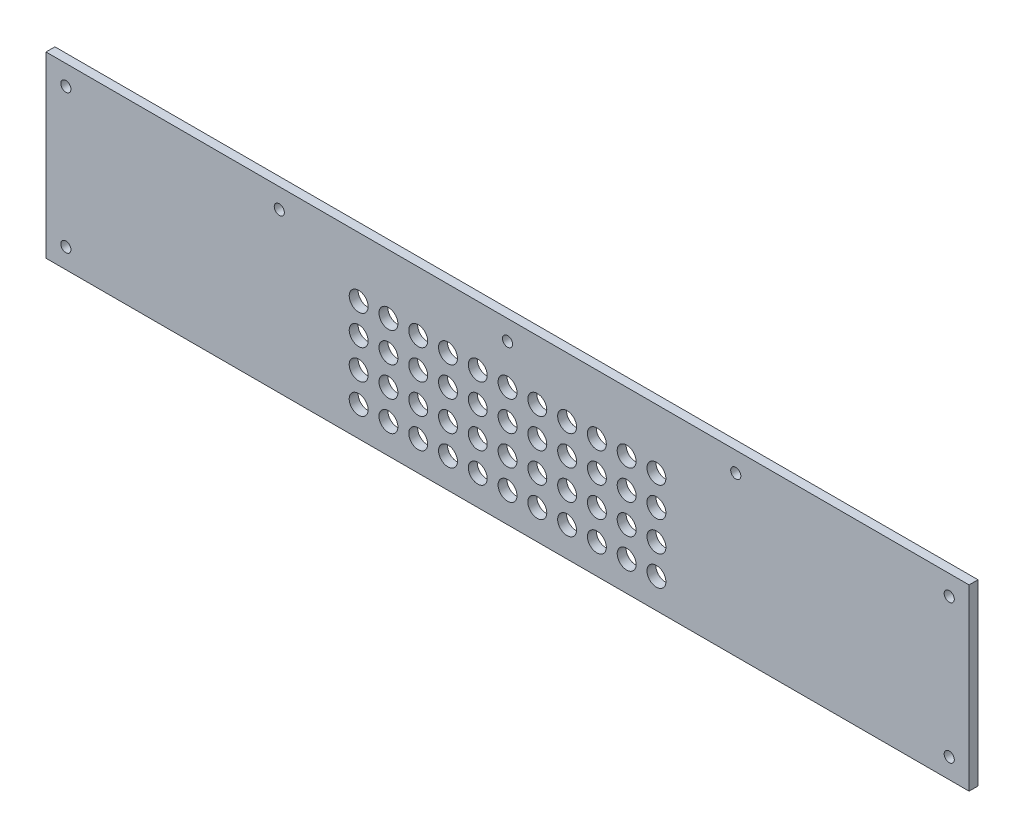
SolidWorks part; units mm, degrees
material "Acrylic (Medium-high impact)"
ref_plane "Front Plane" through (0, 0, 0) normal (0, 0, 1) x (1, 0, 0)
ref_plane "Top Plane" through (0, 0, 0) normal (0, 1, 0) x (1, 0, 0)
ref_plane "Right Plane" through (0, 0, 0) normal (1, 0, 0) x (0, 0, -1)
sketch "Sketch1" plane through (0, 0, 0) normal (0, 0, 1) x (1, 0, 0)
  line L0 (-222.5, 45) -> (-222.5, -45) construction
  line L1 (-232.5, -45) -> (232.5, -45)
  line L2 (-232.5, -45) -> (-232.5, 45)
  line L3 (-232.5, 45) -> (232.5, 45)
  line L4 (232.5, -45) -> (232.5, 45)
  line L5 (-232.5, -45) -> (232.5, 45) construction
  line L6 (-232.5, 45) -> (232.5, -45) construction
  line L7 (0, 45) -> (0, -45) construction
  line L8 (-232.5, 35) -> (2.55, 35) construction
  circle A0 centre (-222.5, 35) radius 2.55
  circle A1 centre (-222.5, -35) radius 2.55
  circle A2 centre (0, 35) radius 2.55
  circle A3 centre (-114.975, 35) radius 2.55
  circle A4 centre (222.5, -35) radius 2.55
  circle A5 centre (222.5, 35) radius 2.55
  circle A6 centre (114.975, 35) radius 2.55
  point P0 (0, 0)
  point P17 (-114.975, 35)
  dimension "D4" = 5.1
  dimension "D5" = 10
  dimension "D6" = 10
  dimension "D7" = 10
  dimension "D1" = 465
  dimension "D2" = 90
  dimension "D3" = 10
extrude "Boss-Extrude1" add sketch "Sketch1" along normal mid plane 4.4958
sketch "Sketch2" plane through (0, 0, 2.2479) normal (0, 0, 1) x (1, 0, 0)
  line L0 (0, 45) -> (0, -45) construction
  line L1 (232.5, 45) -> (-232.5, 45) construction
  line L2 (-232.5, -45) -> (232.5, -45) construction
  circle A0 centre (0, 15) radius 4.7625
  circle A1 centre (15, 15) radius 4.7625
  circle A2 centre (30, 15) radius 4.7625
  circle A3 centre (45, 15) radius 4.7625
  circle A4 centre (60, 15) radius 4.7625
  circle A5 centre (75, 15) radius 4.7625
  circle A6 centre (15, 0) radius 4.7625
  circle A7 centre (30, 0) radius 4.7625
  circle A8 centre (45, 0) radius 4.7625
  circle A9 centre (60, 0) radius 4.7625
  circle A10 centre (75, 0) radius 4.7625
  circle A11 centre (15, -15) radius 4.7625
  circle A12 centre (30, -15) radius 4.7625
  circle A13 centre (45, -15) radius 4.7625
  circle A14 centre (60, -15) radius 4.7625
  circle A15 centre (75, -15) radius 4.7625
  circle A16 centre (15, -30) radius 4.7625
  circle A17 centre (30, -30) radius 4.7625
  circle A18 centre (45, -30) radius 4.7625
  circle A19 centre (60, -30) radius 4.7625
  circle A20 centre (75, -30) radius 4.7625
  circle A21 centre (0, 0) radius 4.7625
  circle A22 centre (0, -15) radius 4.7625
  circle A23 centre (0, -30) radius 4.7625
  circle A24 centre (-75, -30) radius 4.7625
  circle A25 centre (-60, -30) radius 4.7625
  circle A26 centre (-45, -30) radius 4.7625
  circle A27 centre (-30, -30) radius 4.7625
  circle A28 centre (-15, -30) radius 4.7625
  circle A29 centre (-75, -15) radius 4.7625
  circle A30 centre (-60, -15) radius 4.7625
  circle A31 centre (-45, -15) radius 4.7625
  circle A32 centre (-30, -15) radius 4.7625
  circle A33 centre (-15, -15) radius 4.7625
  circle A34 centre (-75, 0) radius 4.7625
  circle A35 centre (-60, 0) radius 4.7625
  circle A36 centre (-45, 0) radius 4.7625
  circle A37 centre (-30, 0) radius 4.7625
  circle A38 centre (-15, 0) radius 4.7625
  circle A39 centre (-75, 15) radius 4.7625
  circle A40 centre (-60, 15) radius 4.7625
  circle A41 centre (-45, 15) radius 4.7625
  circle A42 centre (-30, 15) radius 4.7625
  circle A43 centre (-15, 15) radius 4.7625
  dimension "D1" = 9.525
  dimension "D2" = 30
  dimension "D6" = 15
  dimension "D5" = 15
  dimension "D3" = 6
  dimension "D4" = 4
extrude "Cut-Extrude1" cut sketch "Sketch2" against normal up to next (4.4958 mm away)
